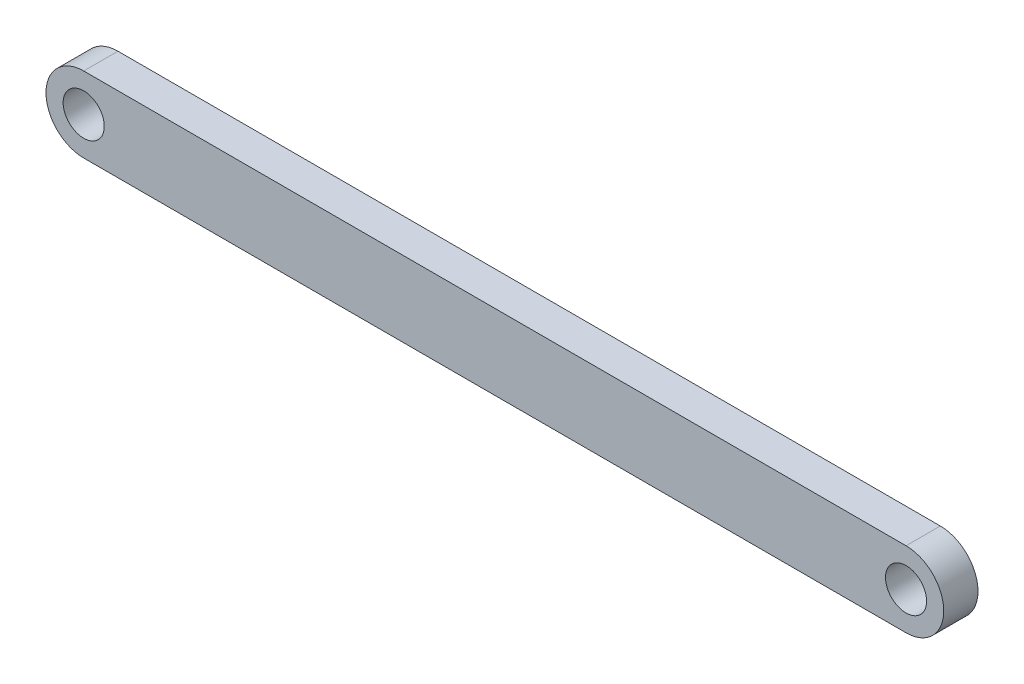
SolidWorks part; units mm, degrees
ref_plane "Front Plane" through (0, 0, 0) normal (0, 0, 1) x (1, 0, 0)
ref_plane "Top Plane" through (0, 0, 0) normal (0, 1, 0) x (1, 0, 0)
ref_plane "Right Plane" through (0, 0, 0) normal (1, 0, 0) x (0, 0, -1)
sketch "Sketch1" plane through (0, 0, 0) normal (0, 0, 1) x (1, 0, 0)
  line L0 (-60, 0) -> (60, 0) construction
  line L1 (-60, 5.5) -> (60, 5.5)
  line L2 (-60, -5.5) -> (60, -5.5)
  arc A0 (-60, 5.5) -> (-60, -5.5) centre (-60, 0) ccw
  arc A1 (60, -5.5) -> (60, 5.5) centre (60, 0) ccw
  circle A2 centre (-60, 0) radius 3
  circle A3 centre (60, 0) radius 3
  point P2 (0, 0)
  dimension "D3" = 6
  dimension "D1" = 11
  dimension "D2" = 120
extrude "Boss-Extrude1" add sketch "Sketch1" along normal mid plane 5
